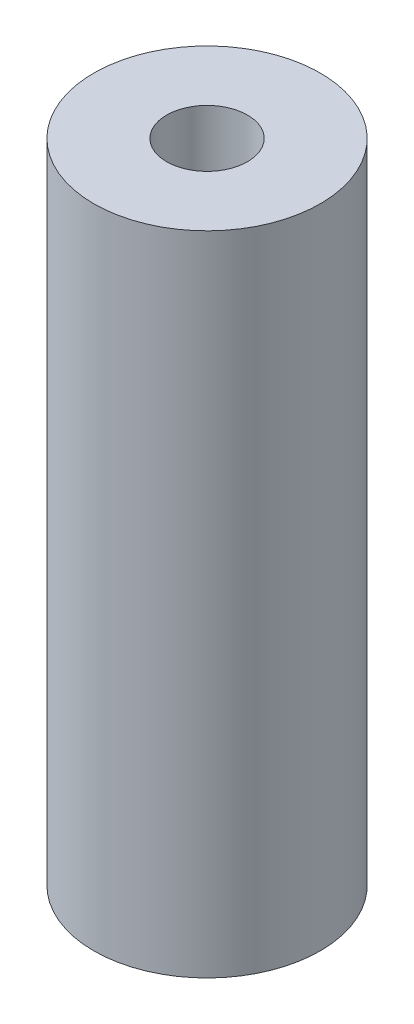
SolidWorks part; units mm, degrees
ref_plane "Front Plane" through (0, 0, 0) normal (0, 0, 1) x (1, 0, 0)
ref_plane "Top Plane" through (0, 0, 0) normal (0, 1, 0) x (1, 0, 0)
ref_plane "Right Plane" through (0, 0, 0) normal (1, 0, 0) x (0, 0, -1)
sketch "Sketch1" plane through (0, 0, 0) normal (0, 1, 0) x (1, 0, 0)
  line L0 (-921.3731, 0) -> (45147.2843, 0) construction
  line L1 (0, -921.3731) -> (0, 45147.2843) construction
  circle A0 centre (0, 0) radius 7
  circle A1 centre (0, 0) radius 2.5
  dimension "D1" = 14
  dimension "D2" = 5
extrude "Boss-Extrude1" add sketch "Sketch1" along normal blind 40
